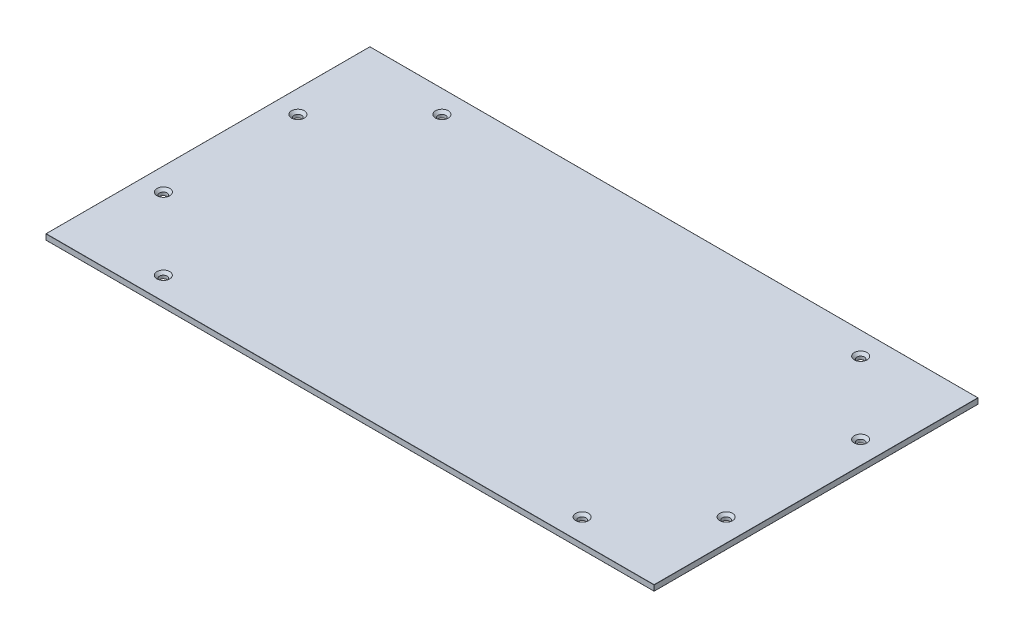
SolidWorks part; units mm, degrees
material "Glass"
ref_plane "Front Plane" through (0, 0, 0) normal (0, 0, 1) x (1, 0, 0)
ref_plane "Top Plane" through (0, 0, 0) normal (0, 1, 0) x (1, 0, 0)
ref_plane "Right Plane" through (0, 0, 0) normal (1, 0, 0) x (0, 0, -1)
sketch "Sketch1" plane through (0, 0, 0) normal (0, 1, 0) x (1, 0, 0)
  line L1 (-321, 171) -> (321, 171)
  line L2 (-321, 171) -> (-321, -171)
  line L3 (-321, -171) -> (321, -171)
  line L4 (321, 171) -> (321, -171)
  line L5 (-321, 171) -> (321, -171) construction
  line L6 (-321, -171) -> (321, 171) construction
  point P0 (0, 0)
  dimension "Largura" = 642
  dimension "Profundidade" = 342
extrude "Boss-Extrude1" add sketch "Sketch1" along normal blind 6
sketch "Sketch2" plane through (0, 6, 0) normal (0, 1, 0) x (1, 0, 0)
  line L0 (-321, -171) -> (321, -171) construction
  line L1 (-321, 171) -> (-321, -171) construction
  line L2 (0, 171) -> (0, -171) construction
  line L3 (321, 171) -> (-321, 171) construction
  line L4 (-321, 0) -> (321, 0) construction
  line L5 (321, -171) -> (321, 171) construction
  circle A0 centre (-221, -147) radius 4
  circle A1 centre (221, -147) radius 4
  circle A2 centre (-297, -71) radius 4
  circle A3 centre (297, -71) radius 4
  circle A4 centre (297, 71) radius 4
  circle A5 centre (221, 147) radius 4
  circle A6 centre (-221, 147) radius 4
  circle A7 centre (-297, 71) radius 4
  dimension "D1" = 8
  dimension "D2" = 24
  dimension "D3" = 100
  dimension "D4" = 24
  dimension "D5" = 100
extrude "Cut-Extrude1" cut sketch "Sketch2" against normal through all
chamfer "Chamfer1" distance 2.75 angle 45 8 edges at (-221, 6, 151) (-297, 6, -75) (-221, 6, -151) (221, 6, -143) (297, 6, -67) (297, 6, 67) (221, 6, 143) (-297, 6, 75)
fillet "Fillet1" radius 0.2 12 edges at (321, 3, -171) (0, 0, -171) (0, 6, -171) (-321, 3, -171) (321, 0, 0) (321, 6, 0) (321, 3, 171) (-321, 0, 0) (-321, 6, 0) (-321, 3, 171) (0, 0, 171) (0, 6, 171)
